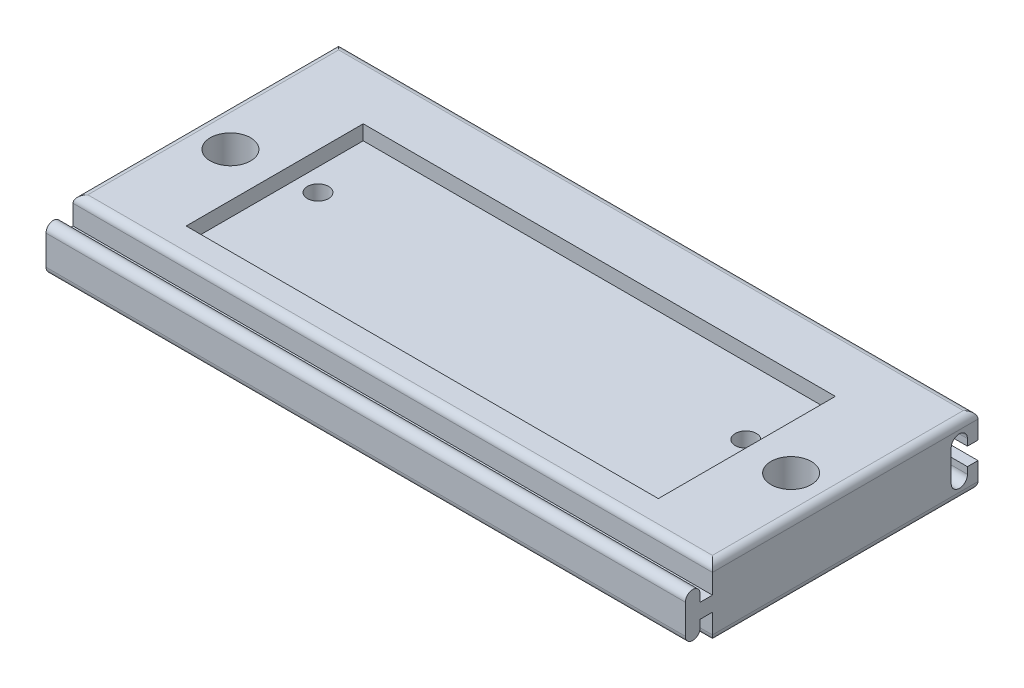
SolidWorks part; units mm, degrees
ref_plane "Front Plane" through (0, 0, 0) normal (0, 0, 1) x (1, 0, 0)
ref_plane "Top Plane" through (0, 0, 0) normal (0, 1, 0) x (1, 0, 0)
ref_plane "Right Plane" through (0, 0, 0) normal (1, 0, 0) x (0, 0, -1)
sketch "Sketch1" plane through (0, 0, 0) normal (0, 1, 0) x (1, 0, 0)
  line L1 (-47.5, 17.5) -> (47.5, 17.5) construction
  line L2 (-47.5, 17.5) -> (-47.5, -17.5) construction
  line L3 (-47.5, -17.5) -> (47.5, -17.5) construction
  line L4 (47.5, 17.5) -> (47.5, -17.5) construction
  line L5 (-47.5, 17.5) -> (47.5, -17.5) construction
  line L6 (-47.5, -17.5) -> (47.5, 17.5) construction
  line L7 (-65, 30) -> (65, 30)
  line L8 (-65, 30) -> (-65, -30)
  line L9 (-65, -30) -> (65, -30)
  line L10 (65, 30) -> (65, -30)
  line L11 (-65, 30) -> (65, -30) construction
  line L12 (-65, -30) -> (65, 30) construction
  circle A0 centre (-43.5, 4.3) radius 2.15
  circle A1 centre (43.5, 4.3) radius 2.15
  circle A4 centre (-57, 0) radius 2.65
  circle A5 centre (57, 0) radius 2.65
  point P0 (0, 0)
  point P10 (0, 0)
  dimension "D6" = 4.3
  dimension "D7" = 4.3
  dimension "D12" = 5.3
  dimension "D13" = 5.3
  dimension "D1" = 35
  dimension "D2" = 95
  dimension "D3" = 87
  dimension "D4" = 4
  dimension "D5" = 13.2
  dimension "D8" = 60
  dimension "D9" = 130
  dimension "D10" = 8
  dimension "D11" = 8
  dimension "D14" = 30
  dimension "D15" = 30
  dimension "D16" = 13.2
extrude "Boss-Extrude1" add sketch "Sketch1" along normal blind 14
sketch "Sketch2" plane through (0, 0, 0) normal (0, -1, 0) x (1, 0, 0)
  line L1 (-39.5776, -5.6766) -> (-40.3467, -1.5914)
  line L2 (-40.3467, -1.5914) -> (-44.269, -0.2148)
  line L3 (-44.269, -0.2148) -> (-47.4224, -2.9234)
  line L4 (-47.4224, -2.9234) -> (-46.6533, -7.0086)
  line L5 (-46.6533, -7.0086) -> (-42.731, -8.3852)
  line L6 (-42.731, -8.3852) -> (-39.5776, -5.6766)
  line L7 (42.815, -8.4001) -> (46.7083, -6.9432)
  line L8 (46.7083, -6.9432) -> (47.3933, -2.8431)
  line L9 (47.3933, -2.8431) -> (44.185, -0.1999)
  line L10 (44.185, -0.1999) -> (40.2917, -1.6568)
  line L11 (40.2917, -1.6568) -> (39.6067, -5.7569)
  line L12 (39.6067, -5.7569) -> (42.815, -8.4001)
  circle A0 centre (-43.5, -4.3) radius 3.6 construction
  circle A1 centre (43.5, -4.3) radius 3.6 construction
  dimension "D1" = 7.2
  dimension "D2" = 7.2
extrude "Cut-Extrude1" cut sketch "Sketch2" against normal blind 7
sketch "Sketch3" plane through (0, 14, 0) normal (0, 1, 0) x (1, 0, 0)
  circle A0 centre (-57, 0) radius 4.1
  circle A1 centre (57, 0) radius 4.1
  dimension "D1" = 8.2
  dimension "D2" = 8.2
extrude "Cut-Extrude2" cut sketch "Sketch3" against normal blind 7
sketch "Sketch4" plane through (0, 14, 0) normal (0, 1, 0) x (1, 0, 0)
  line L1 (-48, 18) -> (48, 18)
  line L2 (-48, 18) -> (-48, -18)
  line L3 (-48, -18) -> (48, -18)
  line L4 (48, 18) -> (48, -18)
  line L5 (-48, 18) -> (48, -18) construction
  line L6 (-48, -18) -> (48, 18) construction
  point P0 (0, 0)
  dimension "D1" = 96
  dimension "D2" = 36
extrude "Cut-Extrude3" cut sketch "Sketch4" against normal blind 3
sketch "Sketch5" plane through (65, 0, 0) normal (1, 0, 0) x (0, 0, -1)
  line L0 (-30, 0) -> (30, 0) construction
  line L1 (18.1, 14) -> (30, 14) construction
  line L2 (18.1, 14) -> (18.1, 0) construction
  line L3 (18.1, 0) -> (30, 0) construction
  line L5 (18.1, 14) -> (30, 0) construction
  line L6 (18.1, 0) -> (30, 14) construction
  line L7 (30, 14) -> (30, 0) construction
  line L8 (-30, 14) -> (30, 14) construction
  line L9 (-30, 14) -> (-18, 14) construction
  line L10 (-30, 14) -> (-30, 0) construction
  line L11 (-30, 0) -> (-18, 0) construction
  line L12 (-18, 14) -> (-18, 0) construction
  line L13 (-30, 14) -> (-18, 0) construction
  line L14 (-30, 0) -> (-18, 14) construction
  line L15 (-30, 14) -> (-30, 0) construction
  line L16 (-24, 14) -> (-24, 8.5)
  line L17 (-28, 10) -> (-28, 4) construction
  line L18 (-26.5, 10) -> (-26.5, 8.5)
  line L19 (-29.5, 10) -> (-29.5, 4)
  line L20 (-26.5, 8.5) -> (-24, 8.5)
  line L21 (-26.5, 5.5) -> (-24, 5.5)
  line L22 (-26.5, 5.5) -> (-26.5, 4)
  line L23 (-24, 5.5) -> (-24, 0)
  line L24 (-24, 14) -> (-30, 14)
  line L25 (-30, 14) -> (-30, 0)
  line L26 (-30, 0) -> (-24, 0) construction
  line L27 (26.2, 10.15) -> (26.2, 3.85) construction
  line L34 (-30, 0) -> (-24, 0)
  line L35 (27.85, 8.8) -> (30, 8.8)
  line L36 (26.2, 10.15) -> (26.2, 3.85) construction
  line L37 (27.85, 10.15) -> (27.85, 8.8)
  line L38 (24.55, 10.15) -> (24.55, 3.85)
  line L39 (30, 8.8) -> (30, 5.2)
  line L40 (30, 5.2) -> (27.85, 5.2)
  line L41 (27.85, 5.2) -> (27.85, 3.85)
  arc A0 (-26.5, 10) -> (-29.5, 10) centre (-28, 10) ccw
  arc A1 (-29.5, 4) -> (-26.5, 4) centre (-28, 4) ccw
  arc A4 (27.85, 10.15) -> (24.55, 10.15) centre (26.2, 10.15) ccw
  arc A5 (24.55, 3.85) -> (27.85, 3.85) centre (26.2, 3.85) ccw
  point P0 (24.05, 7)
  point P9 (-24, 7)
  point P22 (-28, 7)
  point P33 (26.3, 7)
  point P34 (26.4, 7)
  dimension "D1" = 7
  dimension "D2" = 6
  dimension "D3" = 1.8
  dimension "D4" = 7
  dimension "D5" = 12
  dimension "D6" = 0
  dimension "D7" = 6
  dimension "D8" = 3
  dimension "D9" = 4
  dimension "D10" = 1.5
  dimension "D11" = 1.5
  dimension "D12" = 6.3
  dimension "D13" = 7
  dimension "D14" = 3.3
  dimension "D15" = 1.8
  dimension "D16" = 3.8
  dimension "D17" = 0
  dimension "D18" = 0
extrude "Cut-Extrude4" cut sketch "Sketch5" against normal up to surface (130 mm away) up to face at (-65, 7, 0)
fillet "Fillet1" radius 1.5 8 edges at (0, 0, -30) (0, 0, 24) (0, 14, 24) (0, 14, -30) (-65, 0, -3) (-65, 14, -3) (65, 0, -3) (65, 14, -3)
